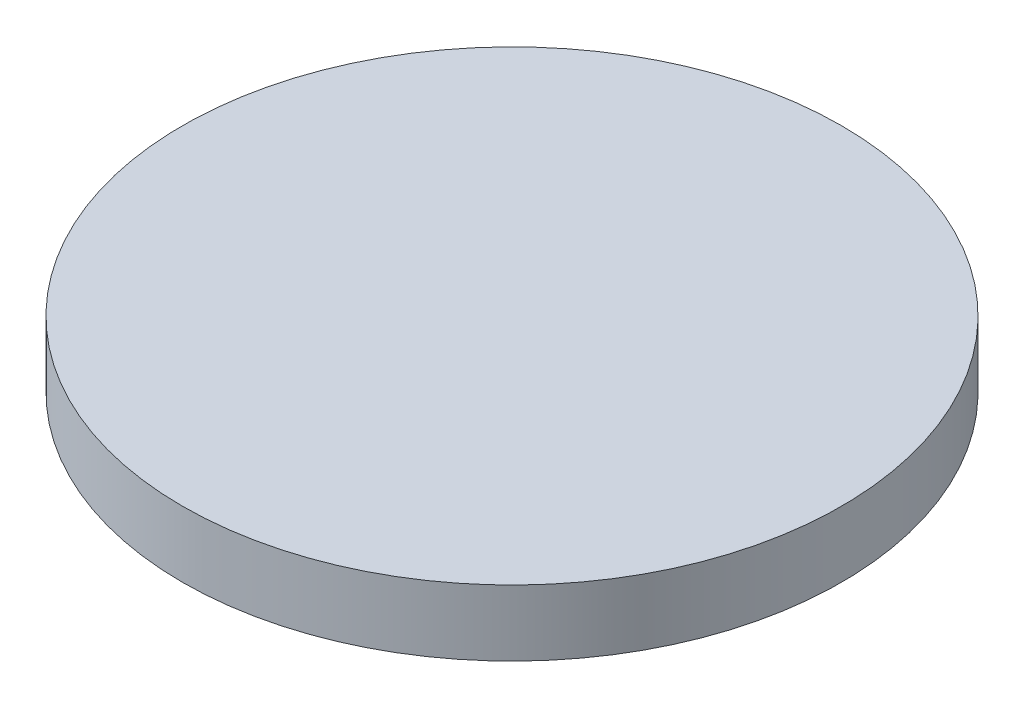
SolidWorks part; units mm, degrees
ref_plane "Front Plane" through (0, 0, 0) normal (0, 0, 1) x (1, 0, 0)
ref_plane "Top Plane" through (0, 0, 0) normal (0, 1, 0) x (1, 0, 0)
ref_plane "Right Plane" through (0, 0, 0) normal (1, 0, 0) x (0, 0, -1)
sketch "Sketch1" plane through (0, 0, 0) normal (0, 1, 0) x (1, 0, 0)
  circle A0 centre (0, 0) radius 40
  dimension "D1" = 80
extrude "Boss-Extrude1" add sketch "Sketch1" along normal mid plane 8
ref_plane "Plane1" through (15, 0, 0) normal (1, 0, 0) x (0, 0, -1)
sketch "Sketch4" plane through (15, 0, 0) normal (1, 0, 0) x (0, 0, -1)
  line L0 (0, 0) -> (0, 3.9739) construction
  line L1 (0, 3.9739) -> (-30, 4)
  line L2 (40, 4) -> (-40, 4) construction
  line L3 (0, 3.9739) -> (30, 4)
  line L4 (-30, 4) -> (8.0118, 69.831)
  circle A0 centre (17.6728, 61.8991) radius 12.5
  circle A1 centre (17.6728, 61.8991) radius 5
  dimension "D3" = 25
  dimension "D4" = 10
  dimension "D1" = 30
  dimension "D2" = 30
  dimension "D5" = 75
